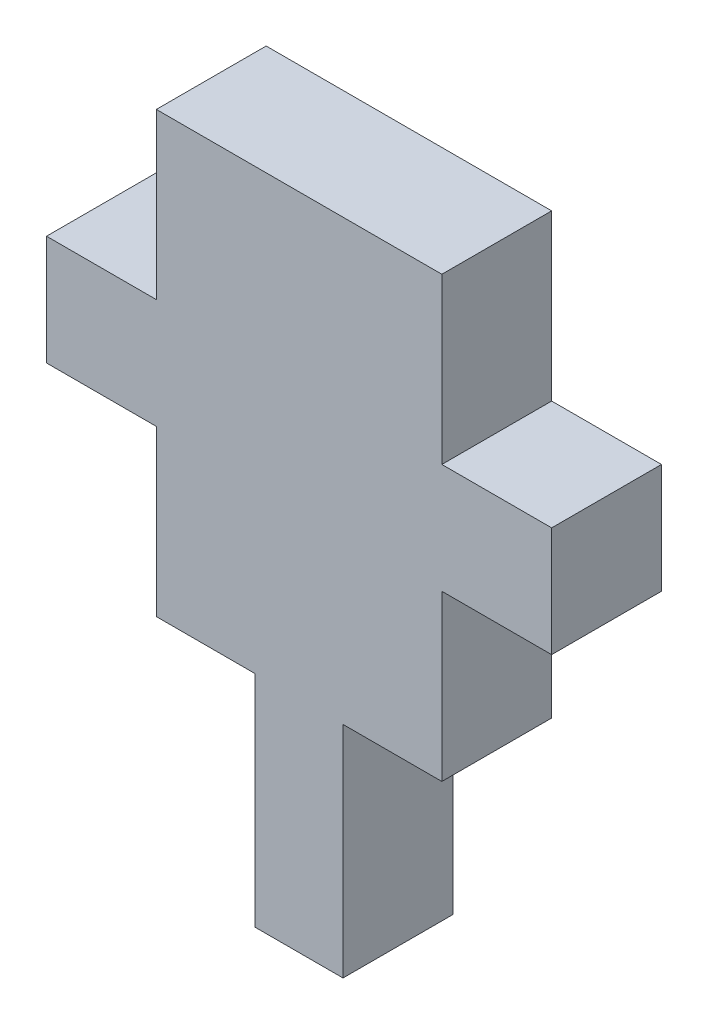
SolidWorks part; units mm, degrees
ref_plane "Plan de face" through (0, 0, 0) normal (0, 0, 1) x (1, 0, 0)
ref_plane "Plan de dessus" through (0, 0, 0) normal (0, 1, 0) x (1, 0, 0)
ref_plane "Plan de droite" through (0, 0, 0) normal (1, 0, 0) x (0, 0, -1)
sketch "Esquisse1" plane through (0, 0, 0) normal (0, 0, 1) x (1, 0, 0)
  line L1 (0, 0) -> (13, 0)
  line L2 (0, 0) -> (0, 20)
  line L3 (0, 20) -> (13, 20)
  line L4 (13, 0) -> (13, 20)
  line L5 (13, 7.5) -> (18, 7.5)
  line L6 (13, 7.5) -> (13, 12.5)
  line L7 (13, 12.5) -> (18, 12.5)
  line L8 (18, 7.5) -> (18, 12.5)
  line L9 (4.5, 0) -> (8.5, 0)
  line L10 (4.5, 0) -> (4.5, -10)
  line L11 (4.5, -10) -> (8.5, -10)
  line L12 (8.5, 0) -> (8.5, -10)
  line L13 (0, 12.5) -> (-5, 12.5)
  line L14 (0, 12.5) -> (0, 7.5)
  line L15 (0, 7.5) -> (-5, 7.5)
  line L16 (-5, 12.5) -> (-5, 7.5)
  dimension "D1" = 20
  dimension "D2" = 13
  dimension "D3" = 7.5
  dimension "D4" = 5
  dimension "D5" = 5
  dimension "D6" = 10
  dimension "D7" = 4
  dimension "D8" = 4.5
  dimension "D9" = 5
  dimension "D10" = 5
  dimension "D11" = 7.5
extrude "Boss.-Extru.1" add sketch "Esquisse1" along normal blind 5 contours L12 L1 L10 L11 | L13 L16 L15 L2 | L1 L4 L3 L2 | L5 L8 L7 L4
